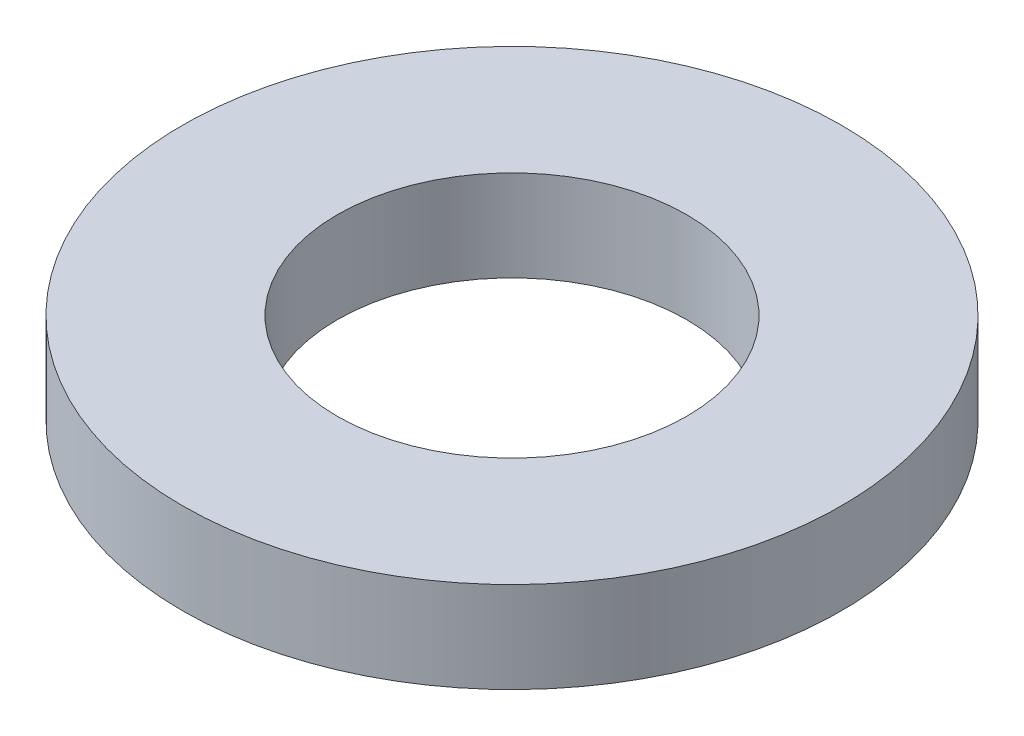
SolidWorks part; units mm, degrees
ref_plane "Front Plane" through (0, 0, 0) normal (0, 0, 1) x (1, 0, 0)
ref_plane "Top Plane" through (0, 0, 0) normal (0, 1, 0) x (1, 0, 0)
ref_plane "Right Plane" through (0, 0, 0) normal (1, 0, 0) x (0, 0, -1)
sketch "Sketch1" plane through (0, 0, 0) normal (0, 1, 0) x (1, 0, 0)
  circle A0 centre (0, 0) radius 6.35
  dimension "OD" = 12.7
extrude "Boss-Extrude1" add sketch "Sketch1" along normal blind 1.7526
sketch "Sketch5" plane through (0, 1.7526, 0) normal (0, 1, 0) x (-1, 0, 0)
  circle A0 centre (0, 0) radius 3.3655
  dimension "ID" = 6.731
extrude "Cut-Extrude1" cut sketch "Sketch5" against normal through all
